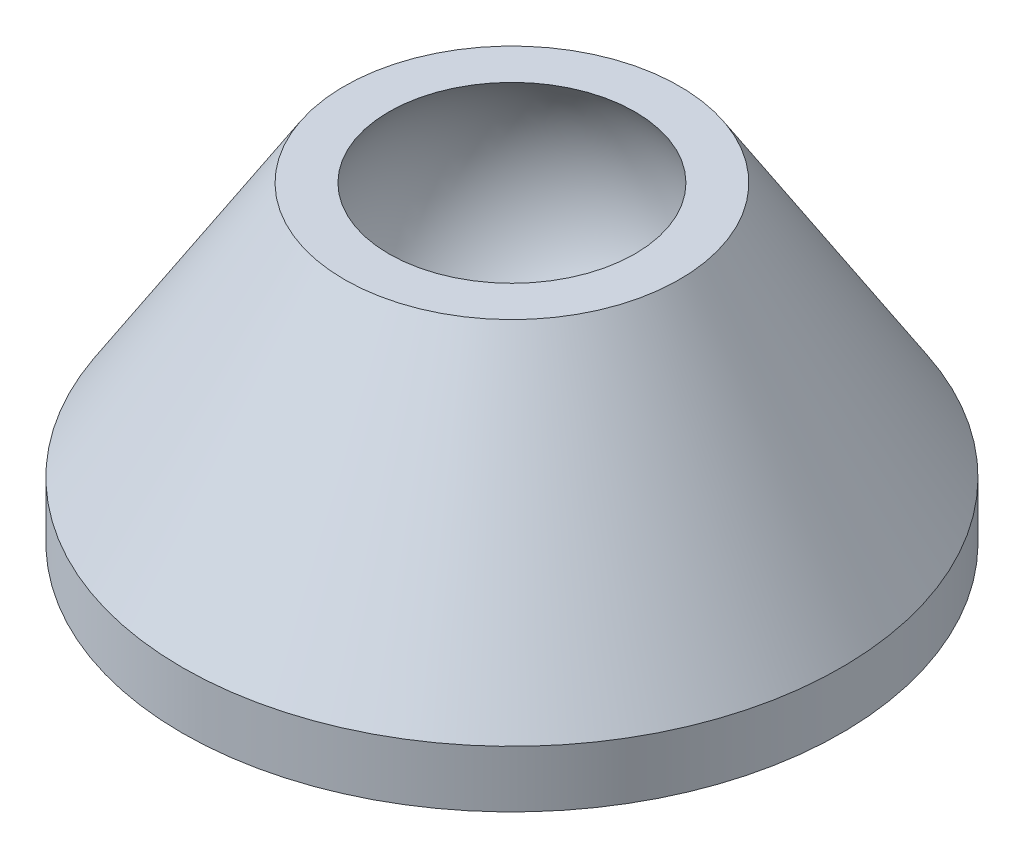
SolidWorks part; units mm, degrees
ref_plane "Front Plane" through (0, 0, 0) normal (0, 0, 1) x (1, 0, 0)
ref_plane "Top Plane" through (0, 0, 0) normal (0, 1, 0) x (1, 0, 0)
ref_plane "Right Plane" through (0, 0, 0) normal (1, 0, 0) x (0, 0, -1)
sketch "Sketch1" plane through (0, 0, 0) normal (0, 0, 1) x (1, 0, 0)
  line L7 (6.456, 3.6754) -> (0, 3.6754)
  line L8 (0, 3.6754) -> (0, 0)
  line L9 (6.456, 3.6754) -> (12.7, -6.1507)
  line L10 (12.7, -6.1507) -> (12.7, -8.34)
  line L11 (0, 0) -> (0, -8.34)
  line L12 (12.7, -8.34) -> (0, -8.34)
  line L13 (11.7442, -8.34) -> (11.7442, -8.5594)
  line L14 (11.2442, -9.0594) -> (0, -9.0594)
  line L15 (0, -9.0594) -> (0, -8.34)
  circle A0 centre (0, 0) radius 6
  arc A1 (11.7442, -8.5594) -> (11.2442, -9.0594) centre (11.2442, -8.5594) cw
  dimension "D1" = 0.5
revolve "Revolve1" add sketch "Sketch1" angle 360 about L11
